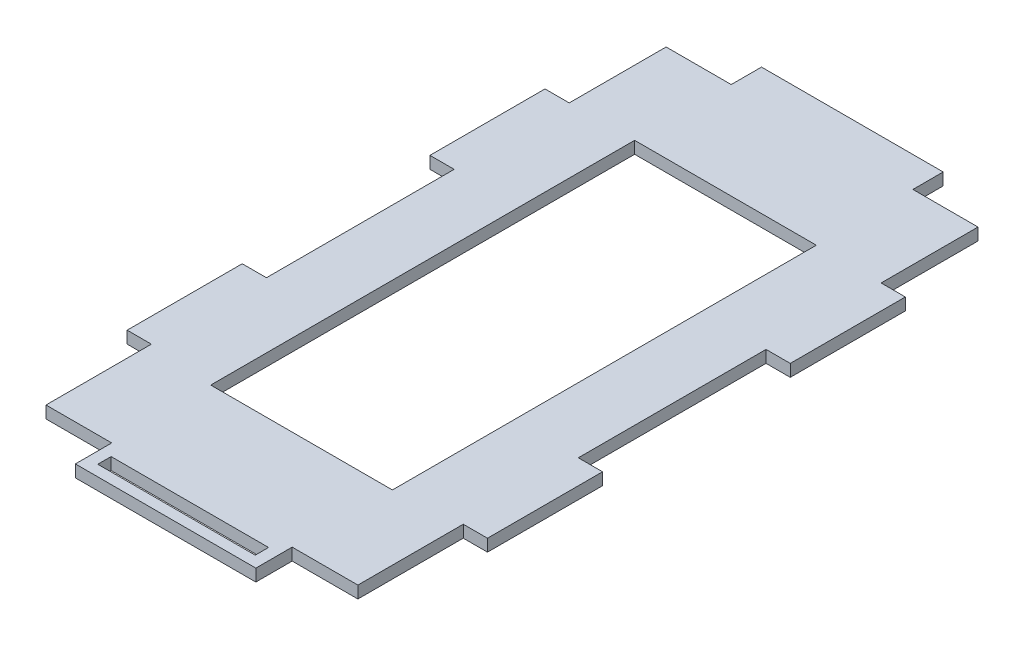
SolidWorks part; units mm, degrees
ref_plane "Ebene vorne" through (0, 0, 0) normal (0, 0, 1) x (1, 0, 0)
ref_plane "Ebene oben" through (0, 0, 0) normal (0, 1, 0) x (1, 0, 0)
ref_plane "Ebene rechts" through (0, 0, 0) normal (1, 0, 0) x (0, 0, -1)
sketch "Skizze3" plane through (0, 0, 0) normal (0, 1, 0) x (1, 0, 0)
  line L0 (-29.8, 0) -> (0, 0)
  line L1 (0, 0) -> (0, 6)
  line L2 (0, 6) -> (10.85, 6)
  line L3 (10.85, 6) -> (10.85, 23.4)
  line L4 (10.85, 23.4) -> (14.85, 23.4)
  line L5 (14.85, 23.4) -> (14.85, 42.4)
  line L6 (14.85, 42.4) -> (10.85, 42.4)
  line L7 (10.85, 42.4) -> (10.85, 73.4)
  line L8 (10.85, 73.4) -> (14.85, 73.4)
  line L9 (14.85, 73.4) -> (14.85, 92.4)
  line L10 (14.85, 92.4) -> (10.85, 92.4)
  line L11 (10.85, 92.4) -> (10.85, 108.4)
  line L13 (-40.65, 108.4) -> (-40.65, 92.4)
  line L14 (-40.65, 92.4) -> (-44.65, 92.4)
  line L15 (-44.65, 92.4) -> (-44.65, 73.4)
  line L16 (-44.65, 73.4) -> (-40.65, 73.4)
  line L17 (-40.65, 73.4) -> (-40.65, 42.4)
  line L18 (-40.65, 42.4) -> (-44.65, 42.4)
  line L19 (-44.65, 42.4) -> (-44.65, 23.4)
  line L20 (-44.65, 23.4) -> (-40.65, 23.4)
  line L21 (-40.65, 23.4) -> (-40.65, 6)
  line L22 (-40.65, 6) -> (-29.8, 6)
  line L23 (-29.8, 6) -> (-29.8, 0)
  line L26 (-29.9, 108.4) -> (-29.9, 113.4)
  line L27 (-29.9, 113.4) -> (0.1, 113.4)
  line L28 (0.1, 108.4) -> (0.1, 113.4)
  line L30 (-40.65, 108.4) -> (-29.9, 108.4)
  line L31 (0.1, 108.4) -> (10.85, 108.4)
  dimension "D1" = 4
  dimension "D2" = 4
  dimension "D3" = 6
  dimension "D4" = 29.8
  dimension "D5" = 16
  dimension "D6" = 19
  dimension "D7" = 5
  dimension "D8" = 19
  dimension "D9" = 31
  dimension "D11" = 30
  dimension "D12" = 102.4
  dimension "D13" = 0
  dimension "D14" = 0
  dimension "D15" = 51.5
  dimension "D16" = 10.75
extrude "Aufsatz-Linear austragen2" add sketch "Skizze3" along normal blind 2
sketch "Skizze4" plane through (0, 2, 0) normal (0, 1, 0) x (1, 0, 0)
  line L0 (-40.65, 73.4) -> (-29.9, 73.4) construction
  line L1 (-29.9, 92.4498) -> (0.1, 92.4498)
  line L2 (-29.9, 92.4498) -> (-29.9, 22.4498)
  line L3 (-29.9, 22.4498) -> (0.1, 22.4498)
  line L4 (0.1, 92.4498) -> (0.1, 22.4498)
  line L5 (10.85, 73.4) -> (0.1, 73.4) construction
  line L6 (-29.9, 92.4498) -> (-29.9, 108.9) construction
  line L7 (-40.65, 6) -> (-29.8, 6) construction
  line L8 (-29.8, 6) -> (-29.9, 22.4498) construction
  line L9 (-27.9, 4) -> (-1.9, 4)
  line L10 (-27.9, 4) -> (-27.9, 1.8)
  line L11 (-27.9, 1.8) -> (-1.9, 1.8)
  line L12 (-1.9, 4) -> (-1.9, 1.8)
  line L13 (-27.9, 4) -> (-29.8, 4) construction
  line L14 (-29.8, 6) -> (-29.8, 0) construction
  line L15 (-1.9, 4) -> (0, 4) construction
  line L16 (0, 0) -> (0, 6) construction
  dimension "D1" = 70
  dimension "D2" = 30
  dimension "D3" = 16.4502
  dimension "D4" = 2
  dimension "D5" = 2.2
  dimension "D6" = 2
extrude "Schnitt-Linear austragen1" cut sketch "Skizze4" against normal up to surface (2 mm away) up to face at (-14.9, 0, -57.5286)
